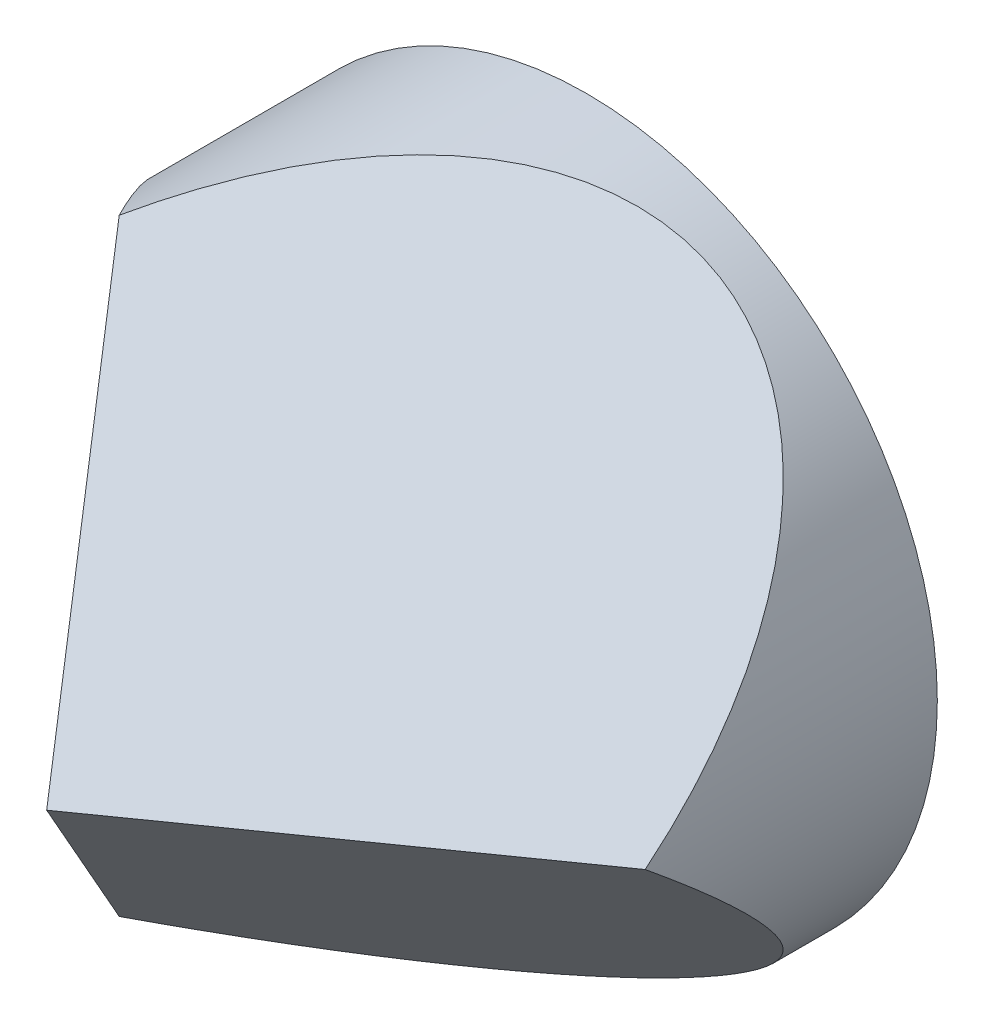
SolidWorks part; units mm, degrees
ref_plane "前视基准面" through (0, 0, 0) normal (0, 0, 1) x (1, 0, 0)
ref_plane "上视基准面" through (0, 0, 0) normal (0, 1, 0) x (1, 0, 0)
ref_plane "右视基准面" through (0, 0, 0) normal (1, 0, 0) x (0, 0, -1)
sketch "草图1" plane through (0, 0, 0) normal (0, 0, 1) x (1, 0, 0)
  circle A0 centre (0, 0) radius 31.1
  dimension "D1" = 62.2
extrude "凸台-拉伸1" add sketch "草图1" along normal blind 47.9
sketch "草图2" plane through (0, 0, 0) normal (0, 1, 0) x (1, 0, 0)
  line L0 (0, 0) -> (0, -47.9) construction
  line L1 (-31.1, -47.9) -> (31.1, -47.9) construction
  line L2 (0, -47.9) -> (-40.6903, 9.6329)
  line L3 (-40.6903, 9.6329) -> (-40.6903, -56.657)
  line L4 (-40.6903, -56.657) -> (0, -56.657)
  line L5 (0, -56.657) -> (0, -47.9)
  line L6 (31.1, 0) -> (-31.1, 0) construction
  dimension "D1" = 54.73
extrude "切除-拉伸1" cut sketch "草图2" against normal mid plane 79
sketch "草图3" plane through (0, 0, 47.9) normal (0, 0, 1) x (1, 0, 0)
  line L0 (0, 0) -> (16.7186, 0)
  line L1 (0, 0) -> (8.0189, 13.8892)
  line L2 (0, 0) -> (8.0629, -13.9654)
  dimension "D1" = 60
  dimension "D2" = 60
ref_plane "基准面1" through (0, 0, 0) normal (0.866, -0.5, 0) x (0.5, 0.866, 0)
ref_plane "基准面2" through (0, 0, 0) normal (-0.866, -0.5, 0) x (0.5, -0.866, 0)
sketch "草图4" plane through (0, 0, 0) normal (0.866, -0.5, 0) x (0.5, 0.866, 0)
  line L0 (0, 0) -> (0, 22.6417) construction
  line L2 (0, 47.9) -> (100.6993, -94.4808)
  line L3 (0, 47.9) -> (8.3593, 47.9) construction
  line L5 (100.6993, -94.4808) -> (100.6993, 79.0892)
  line L6 (100.6993, 79.0892) -> (0, 79.0892)
  line L7 (0, 79.0892) -> (0, 47.9)
  line L8 (-31.1, 0) -> (31.1, 0) construction
  dimension "D1" = 54.73
extrude "切除-拉伸2" cut sketch "草图4" along normal mid plane 124
sketch "草图5" plane through (0, 0, 0) normal (-0.866, -0.5, 0) x (0.5, -0.866, 0)
  line L0 (0, 47.9) -> (45.6903, -16.7024)
  line L1 (0, 47.9) -> (16.1259, 47.9) construction
  line L2 (45.6903, -16.7024) -> (45.6903, 62.0813)
  line L3 (45.6903, 62.0813) -> (2.6847, 62.0813)
  line L4 (2.6847, 62.0813) -> (0, 47.9)
  line L5 (-31.1, 0) -> (31.1, 0) construction
  dimension "D1" = 54.73
extrude "切除-拉伸3" cut sketch "草图5" against normal mid plane 107
